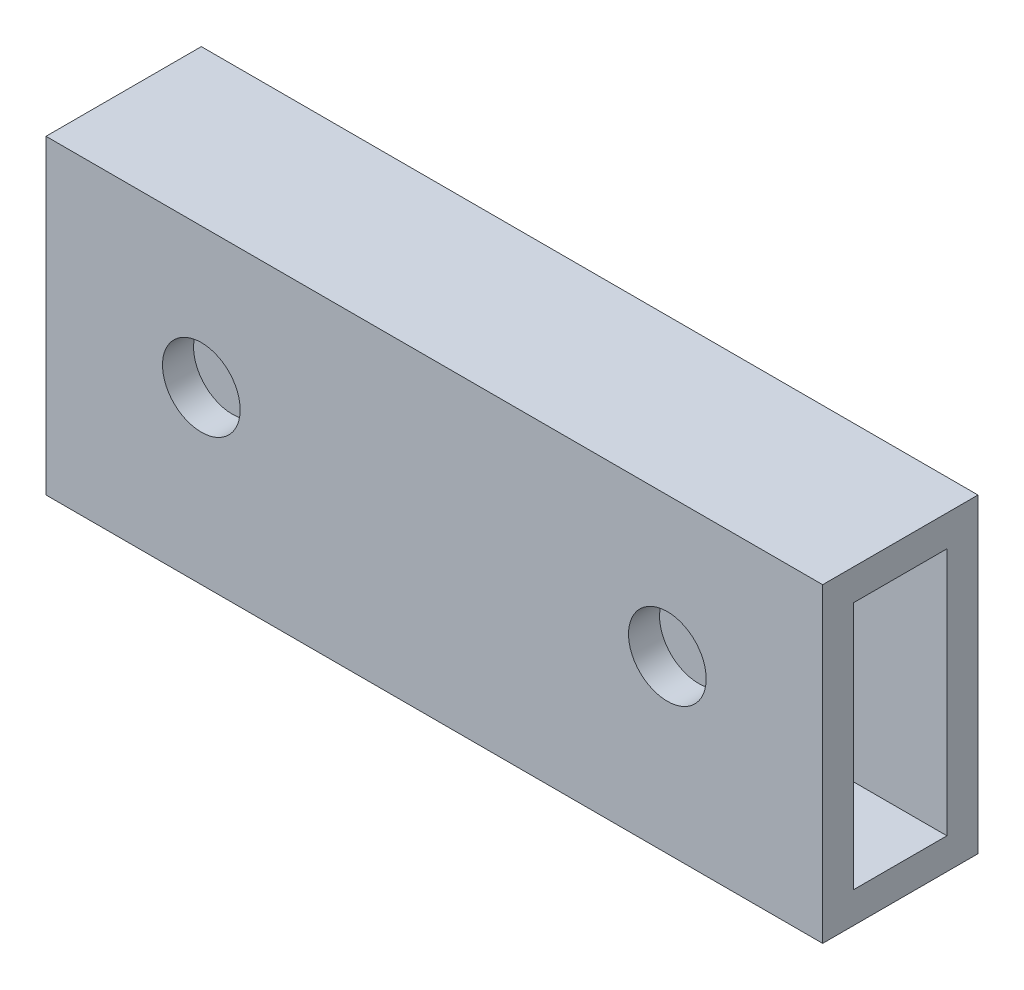
SolidWorks part; units mm, degrees
ref_plane "Front Plane" through (0, 0, 0) normal (0, 0, 1) x (1, 0, 0)
ref_plane "Top Plane" through (0, 0, 0) normal (0, 1, 0) x (1, 0, 0)
ref_plane "Right Plane" through (0, 0, 0) normal (1, 0, 0) x (0, 0, -1)
sketch "Sketch1" plane through (0, 0, 0) normal (0, 0, 1) x (1, 0, 0)
  line L0 (-96.1387, 84.334) -> (-96.1387, 131.334) construction
  line L1 (-96.1387, 114.334) -> (-46.1387, 114.334)
  line L2 (-96.1387, 114.334) -> (-96.1387, 134.334)
  line L3 (-96.1387, 134.334) -> (-46.1387, 134.334)
  line L4 (-46.1387, 114.334) -> (-46.1387, 134.334)
  line L5 (-46.1387, 131.334) -> (-46.1387, 84.334) construction
  line L6 (-93.1387, 134.334) -> (-49.1387, 134.334) construction
  dimension "D1" = 20
extrude "Extrude1" add sketch "Sketch1" along normal blind 10
sketch "Sketch2" plane through (-96.1387, 0, 0) normal (-1, 0, 0) x (0, 0, 1)
  line L0 (10, 134.334) -> (10, 114.334) construction
  line L1 (8, 132.334) -> (2, 132.334)
  line L2 (8, 132.334) -> (8, 116.334)
  line L3 (8, 116.334) -> (2, 116.334)
  line L4 (2, 132.334) -> (2, 116.334)
  line L5 (10, 114.334) -> (0, 114.334) construction
  line L6 (10, 134.334) -> (0, 134.334) construction
  line L7 (0, 134.334) -> (0, 114.334) construction
  dimension "D1" = 2
  dimension "D2" = 2
  dimension "D3" = 2
  dimension "D4" = 2
extrude "Cut-Extrude1" cut sketch "Sketch2" against normal blind 60
sketch "Sketch3" plane through (0, 0, 10) normal (0, 0, 1) x (1, 0, 0)
  arc A0 (-56.1387, 127.834) -> (-56.1387, 122.834) centre (-56.1387, 125.334) ccw construction
  arc A1 (-56.1387, 122.834) -> (-56.1387, 127.834) centre (-56.1387, 125.334) ccw construction
  arc A2 (-86.1387, 127.834) -> (-86.1387, 122.834) centre (-86.1387, 125.334) ccw construction
  arc A3 (-86.1387, 122.834) -> (-86.1387, 127.834) centre (-86.1387, 125.334) ccw construction
  arc A4 (-56.1387, 127.834) -> (-56.1387, 122.834) centre (-56.1387, 125.334) ccw
  arc A5 (-56.1387, 122.834) -> (-56.1387, 127.834) centre (-56.1387, 125.334) ccw
  arc A6 (-86.1387, 127.834) -> (-86.1387, 122.834) centre (-86.1387, 125.334) ccw
  arc A7 (-86.1387, 122.834) -> (-86.1387, 127.834) centre (-86.1387, 125.334) ccw
extrude "Cut-Extrude2" cut sketch "Sketch3" against normal blind 30
